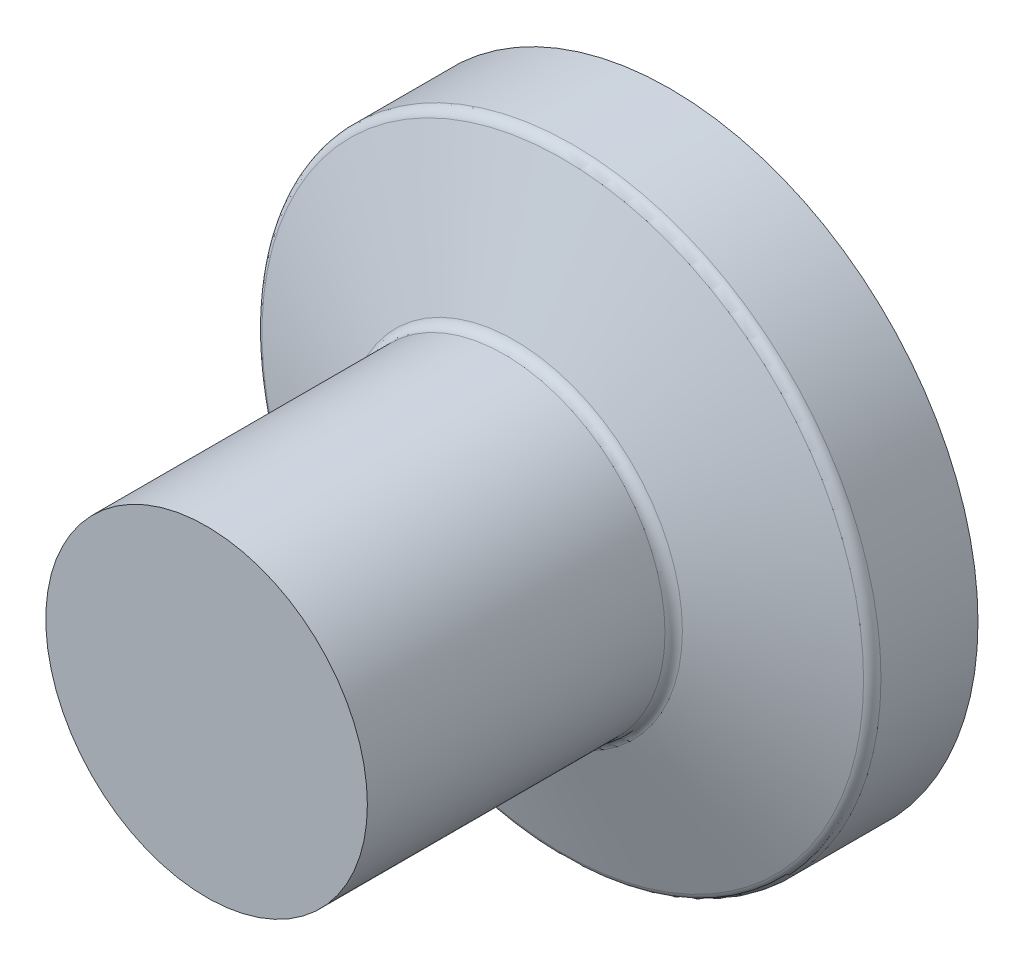
SolidWorks part; units mm, degrees
ref_plane "Front Plane" through (0, 0, 0) normal (0, 0, 1) x (1, 0, 0)
ref_plane "Top Plane" through (0, 0, 0) normal (0, 1, 0) x (1, 0, 0)
ref_plane "Right Plane" through (0, 0, 0) normal (1, 0, 0) x (0, 0, -1)
sketch "Sketch1" plane through (0, 0, 0) normal (1, 0, 0) x (0, 0, -1)
  line L0 (0, 0) -> (0, 14.75)
  line L1 (0, 55) -> (0, -55) construction
  line L2 (0, 14.75) -> (27.2998, 14.75)
  line L3 (28.2395, 15.408) -> (32.6741, 27.592)
  line L4 (33.6138, 28.25) -> (42.5136, 28.25)
  line L5 (0, 0) -> (52, 0)
  line L6 (55, 0) -> (-55, 0) construction
  line L7 (42.5136, 28.25) -> (42.5136, 24.25)
  arc A0 (42.5136, 24.25) -> (52, 0) centre (16.2618, 0) cw
  arc A1 (33.6138, 28.25) -> (32.6741, 27.592) centre (33.6138, 27.25) ccw
  arc A2 (28.2395, 15.408) -> (27.2998, 14.75) centre (27.2998, 15.75) cw
  point P17 (32.9136, 28.25)
  point P20 (28, 14.75)
  dimension "D8" = 1
  dimension "D1" = 28
  dimension "D2" = 28.25
  dimension "D3" = 14.75
  dimension "D4" = 24
  dimension "D5" = 9.6
  dimension "D6" = 70
  dimension "D7" = 4
revolve "Revolve1" add sketch "Sketch1" angle 360 about L5
